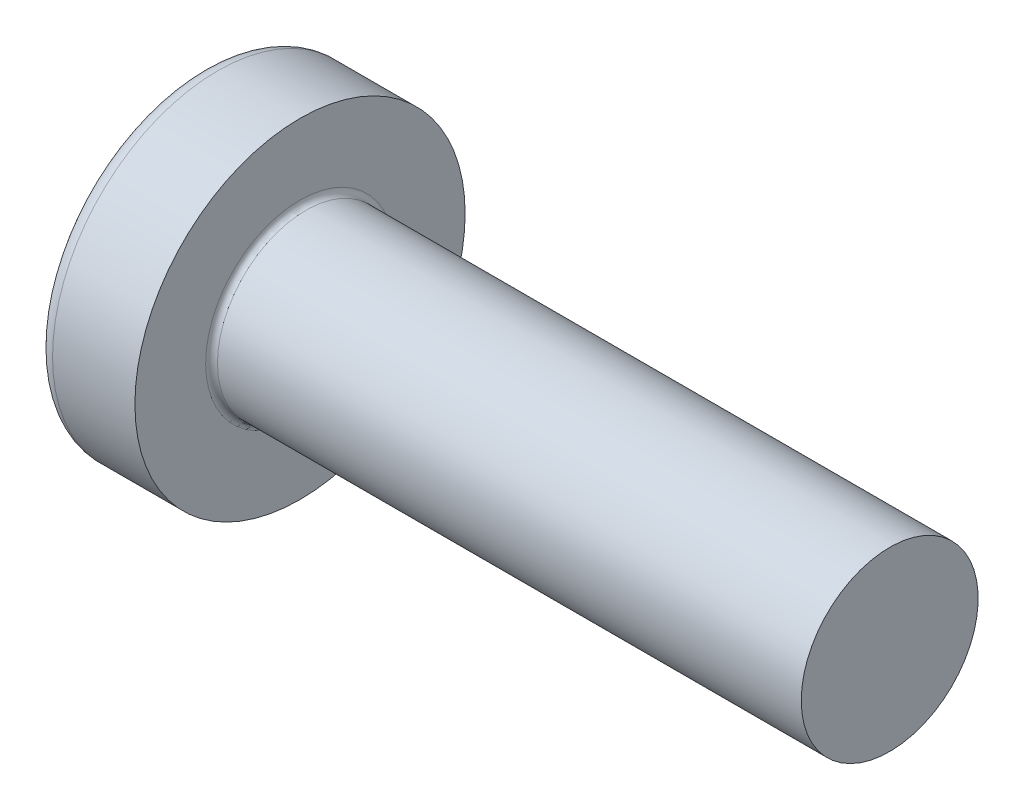
SolidWorks part; units mm, degrees
ref_plane "Plane1" through (0, 0, 0) normal (0, 0, 1) x (1, 0, 0)
ref_plane "Plane2" through (0, 0, 0) normal (0, 1, 0) x (1, 0, 0)
ref_plane "Plane3" through (0, 0, 0) normal (1, 0, 0) x (0, 0, -1)
sketch "BodySke" plane through (0, 0, 0) normal (0, 0, 1) x (1, 0, 0)
  line L0 (2.4, 1.5) -> (2.4, 2.8)
  line L1 (2.65, 6.35) -> (2.65, -3.175) construction
  line L2 (-25.4, 0) -> (127, 0) construction
  line L3 (12.4, 0) -> (0, 0)
  line L4 (2.4, 1.5) -> (12.4, 1.5)
  line L5 (12.4, 1.5) -> (12.4, 0)
  line L6 (1.0035, 2.8) -> (2.4, 2.8)
  line L8 (2.4, 6.35) -> (2.4, -3.175) construction
  arc A0 (0.7754, 2.6744) -> (0, 0) centre (5, 0) ccw
  arc A2 (0.7754, 2.6744) -> (1.0035, 2.8) centre (1.0035, 2.53) cw
  dimension "Head_fillet_rad" = 0.27
  dimension "Head_crown_rad" = 5
  dimension "Head_ht" = 2.4
  dimension "Diameter" = 3
  dimension "Length" = 10
  dimension "Head_dia" = 5.6
  dimension "Advance" = 0.5
  dimension "Thread_nom" = 10
revolve "Base-Revolve" add sketch "BodySke"
cosmetic thread "ThreadCosmetic" [suppressed]
fillet "Fillet1" radius 0.1 1 edges at (2.4, 0, 1.5)
sketch "Sketch3" plane through (0, 0, 0) normal (1, 0, 0) x (0, 0, -1)
  line L0 (0.37, -1.4) -> (-0.37, -1.4)
  line L1 (0.37, -1.4) -> (0.37, 1.4)
  line L2 (-0.37, 1.4) -> (0.37, 1.4)
  line L3 (-0.37, 1.4) -> (-0.37, -1.4)
  dimension "D1" = 1.4
  dimension "Cross_dia" = 2.8
  dimension "D2" = 0.37
  dimension "Cross_width" = 0.74
ref_plane "Plane4" through (1.75, 0, 0) normal (1, 0, 0) x (0, 0, -1)
sketch "Sketch4" plane through (1.75, 0, 0) normal (1, 0, 0) x (0, 0, -1)
  line L0 (0.37, -0.5275) -> (-0.37, -0.5275)
  line L1 (0.37, -0.5275) -> (0.37, 0.5275)
  line L2 (-0.37, 0.5275) -> (0.37, 0.5275)
  line L3 (-0.37, 0.5275) -> (-0.37, -0.5275)
  dimension "D1" = 0.74
  dimension "D2" = 1.055
  dimension "D3" = 0.37
  dimension "D4" = 0.5275
loft "Recess" cut profiles "Sketch3", "Sketch4"
pattern_circular "RecPat" count 2 every 90 about axis through (0, 0, 0) along (1, 0, 0) of "Recess"
sketch "RecCorSke" plane through (0, 0, 0) normal (0, 0, 1) x (1, 0, 0)
  line L0 (-3.175, 0) -> (15.875, 0) construction
  line L1 (-25.4, 0) -> (127, 0) construction
  line L2 (0, 0) -> (0, 0.6784)
  line L3 (0, 0.6784) -> (1.75, 0.556)
  line L4 (1.75, 0.556) -> (1.9307, 0)
  line L5 (1.9307, 0) -> (0, 0)
  dimension "Diameter" = 1.112
  dimension "Depth" = 1.75
  dimension "Draft_angle" = 4
  dimension "Bottom_angle" = 18
revolve "RecessCore" cut sketch "RecCorSke" angle 360 about L0
sketch "ThdSchSke" plane through (0, 0, 0) normal (0, 0, 1) x (1, 0, 0)
  line L0 (3.4, -1.2195) -> (3.2036, -1.5)
  line L1 (3.4, -1.2195) -> (3.5964, -1.5)
  line L2 (3.5964, -1.5) -> (3.5964, -1.875)
  line L3 (-3.175, 0) -> (5.1513, 0) construction
  line L5 (3.5964, -1.875) -> (3.2036, -1.875)
  line L6 (3.2036, -1.875) -> (3.2036, -1.5)
  dimension "Thread_minor" = 2.439
  dimension "Diameter" = 3
  dimension "Start" = 3.4
  dimension "SideAngle" = 55
  dimension "VeeAngle" = 70
  dimension "Overcut" = 3.75
revolve "ThreadSchematic" [suppressed] cut sketch "ThdSchSke" angle 360 about L3
pattern_linear "ThdSchPat" [suppressed]
equation "\"D1@Sketch3\" = \"Cross_dia@Sketch3\" / 2"
equation "\"D2@Sketch3\" = \"Cross_width@Sketch3\" / 2"
equation "\"Depth@RecCorSke\" = \"Cross_depth@Plane4\""
equation "\"D1@Sketch4\" = \"Cross_width@Sketch3\""
equation "\"D2@Sketch4\" = \"Cross_dia@Sketch3\" - 2.0 * \"Cross_depth@Plane4\" * tan(26.5  * 0.017453292)"
equation "\"D3@Sketch4\" = \"D1@Sketch4\" / 2"
equation "\"D4@Sketch4\" = \"D2@Sketch4\" / 2"
equation "\"Thread_length@ThreadCosmetic\" = ((sgn( (\"Length@BodySke\" - \"Advance@BodySke\" * 2.0 ) - \"Thread_nom@BodySke\" )-1)*( (\"Length@BodySke\" - \"Advance@BodySke\" * 2.0 ) - \"Thread_nom@BodySke\" ))/-2+ \"Thread_nom@BodySke\""
equation "\"Thread_minor@ThdSchSke\" = \"Thread_minor@ThreadCosmetic\""
equation "\"Diameter@ThdSchSke\" = \"Diameter@BodySke\""
equation "\"Overcut@ThdSchSke\" = \"Diameter@BodySke\" * 1.25"
equation "\"Start@ThdSchSke\" = \"Head_ht@BodySke\" + \"Length@BodySke\" - \"Thread_length@ThreadCosmetic\"  '---Non-countersunk---"
equation "\"Num_threads@ThdSchPat\" = int( \"Thread_length@ThreadCosmetic\" / \"Advance@BodySke\" + 0.999 )  + 1"
equation "\"Advance@ThdSchPat\" = \"Thread_length@ThreadCosmetic\" /  (\"Num_threads@ThdSchPat\" - 1) 'relax it"
